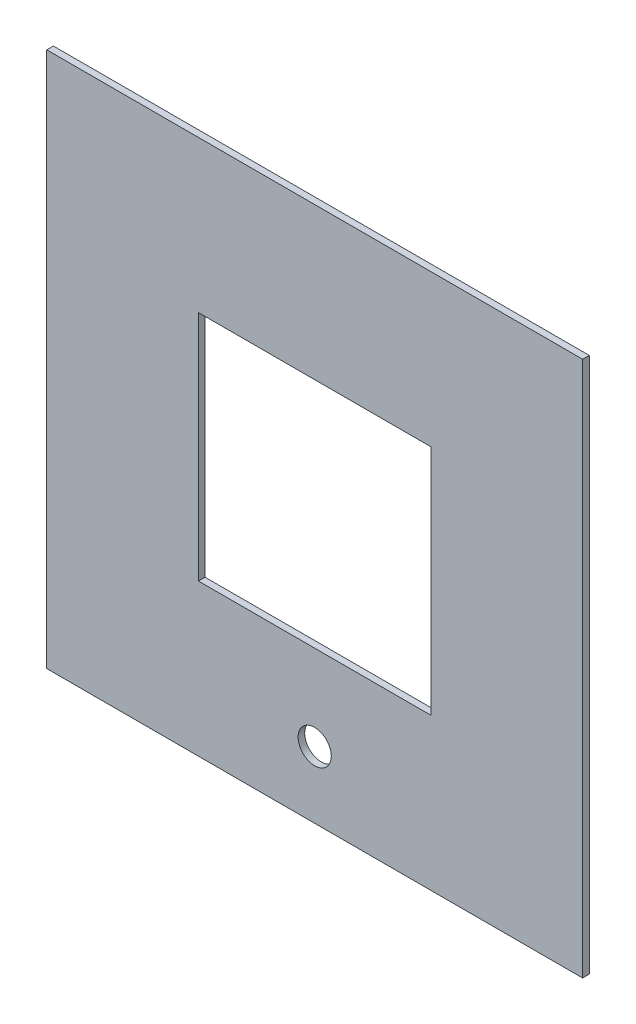
SolidWorks part; units mm, degrees
ref_plane "Alzado" through (0, 0, 0) normal (0, 0, 1) x (1, 0, 0)
ref_plane "Planta" through (0, 0, 0) normal (0, 1, 0) x (1, 0, 0)
ref_plane "Vista lateral" through (0, 0, 0) normal (1, 0, 0) x (0, 0, -1)
sketch "Sketch1" plane through (0, 0, 0) normal (0, 0, 1) x (1, 0, 0)
  line L1 (-121, 121) -> (121, 121)
  line L2 (-121, 121) -> (-121, -121)
  line L3 (-121, -121) -> (121, -121)
  line L4 (121, 121) -> (121, -121)
  line L5 (-121, 121) -> (121, -121) construction
  line L6 (-121, -121) -> (121, 121) construction
  line L7 (-52.5, 52.5) -> (52.5, 52.5)
  line L8 (-52.5, 52.5) -> (-52.5, -52.5)
  line L9 (-52.5, -52.5) -> (52.5, -52.5)
  line L10 (52.5, 52.5) -> (52.5, -52.5)
  line L11 (-52.5, 52.5) -> (52.5, -52.5) construction
  line L12 (-52.5, -52.5) -> (52.5, 52.5) construction
  point P0 (0, 0)
  point P6 (0, 0)
  dimension "D1" = 242
  dimension "D2" = 242
  dimension "D3" = 105
extrude "Boss-Extrude1" add sketch "Sketch1" along normal blind 3
sketch "Sketch2" plane through (0, 0, 3) normal (0, 0, 1) x (1, 0, 0)
  circle A0 centre (0, -91) radius 7.5
  dimension "D1" = 15
extrude "Cut-Extrude1" cut sketch "Sketch2" against normal up to next
